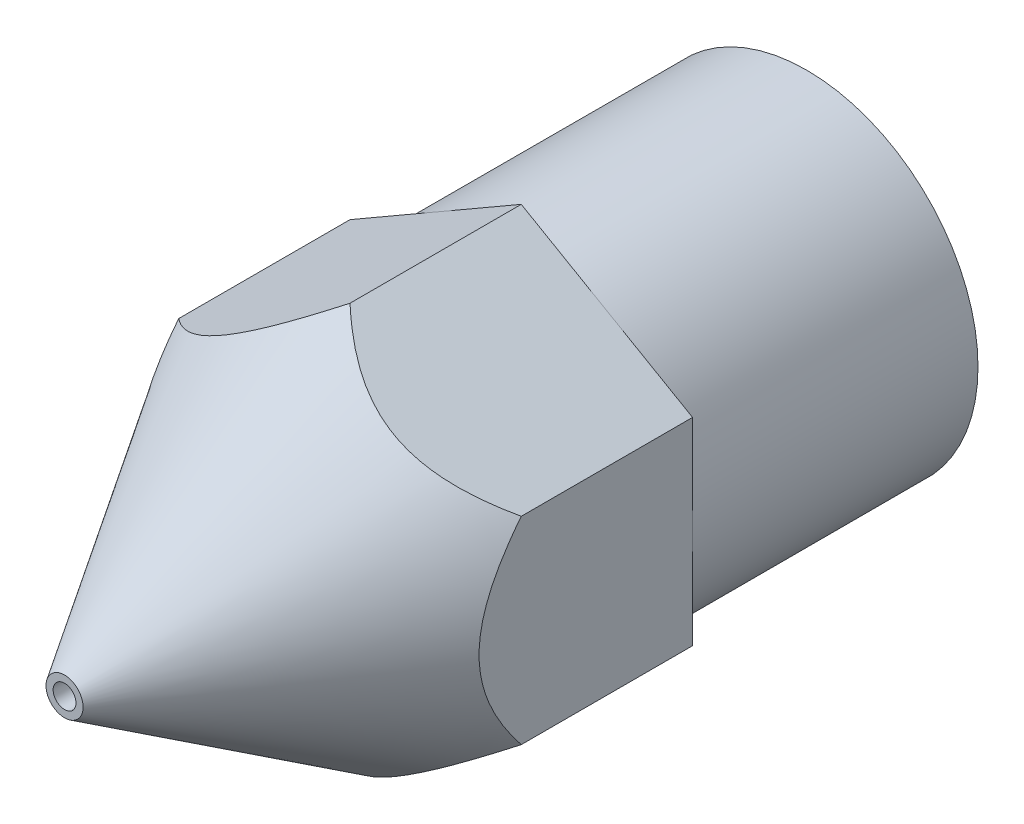
SolidWorks part; units mm, degrees
material "Brass"
ref_plane "Front Plane" through (0, 0, 0) normal (0, 0, 1) x (1, 0, 0)
ref_plane "Top Plane" through (0, 0, 0) normal (0, 1, 0) x (1, 0, 0)
ref_plane "Right Plane" through (0, 0, 0) normal (1, 0, 0) x (0, 0, -1)
sketch "Sketch4" plane through (0, 0, 0) normal (0, 0, 1) x (1, 0, 0)
  line L1 (0, 3.4641) -> (-3, 1.7321)
  line L2 (-3, 1.7321) -> (-3, -1.7321)
  line L3 (-3, -1.7321) -> (0, -3.4641)
  line L4 (0, -3.4641) -> (3, -1.7321)
  line L5 (3, -1.7321) -> (3, 1.7321)
  line L6 (3, 1.7321) -> (0, 3.4641)
  circle A0 centre (0, 0) radius 3 construction
  dimension "D1" = 6
sketch "Sketch1" plane through (0, 0, 0) normal (1, 0, 0) x (0, 0, -1)
  line L0 (0, 0.2) -> (0, 0.325)
  line L1 (0, 0.325) -> (5, 3.4641)
  line L2 (5, 3.4641) -> (8, 3.4641)
  line L3 (8, 3.4641) -> (8, 3)
  line L4 (8, 3) -> (13, 3)
  line L5 (13, 3) -> (13, 1)
  line L6 (13, 1) -> (3, 1)
  line L7 (3, 1) -> (0.5, 0.2)
  line L8 (0.5, 0.2) -> (0, 0.2)
  line L9 (0, 0) -> (13, 0) construction
  dimension "D1" = 0.2
  dimension "D2" = 8
  dimension "D3" = 13
  dimension "D4" = 1
  dimension "D6" = 0.5
  dimension "D7" = 3
  dimension "D8" = 3
  dimension "D9" = 0.325
  dimension "D10" = 10
revolve "Revolve2" add sketch "Sketch1" angle 360 about L9
extrude "Cut-Extrude5" cut sketch "Sketch4" against normal through all flip side to cut
